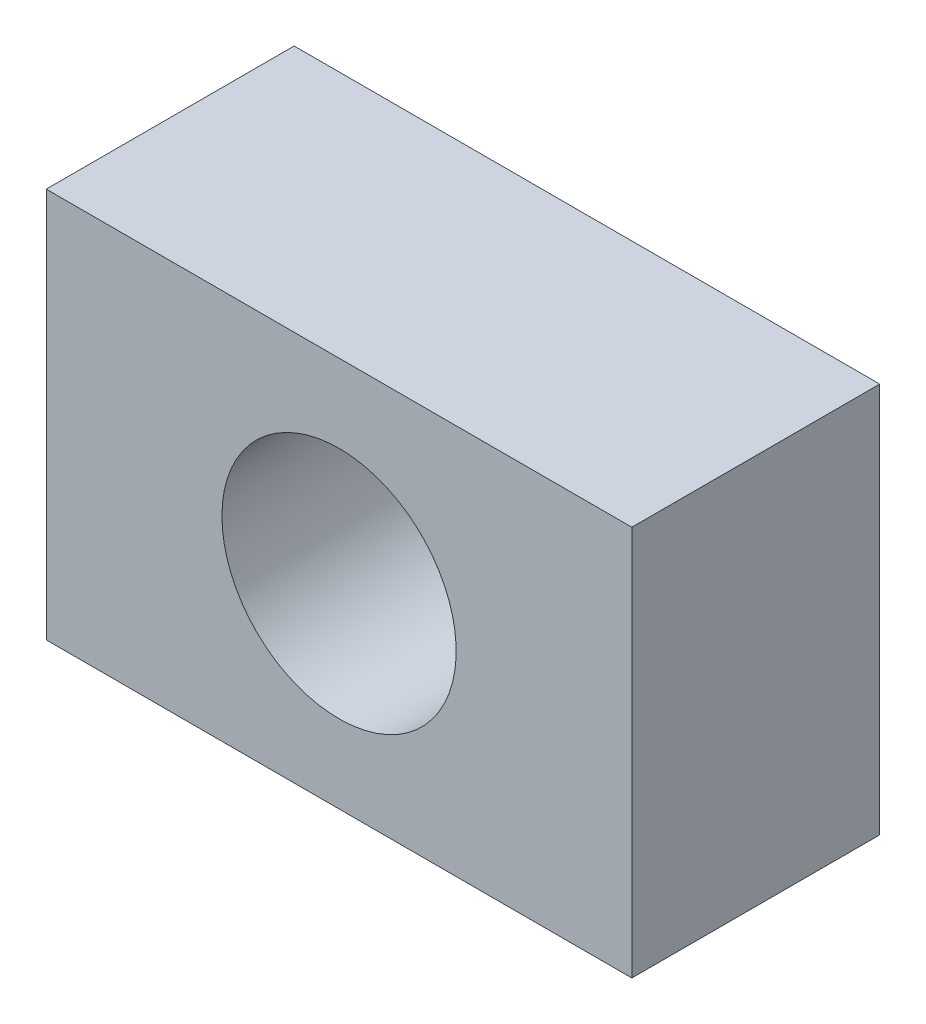
SolidWorks part; units mm, degrees
material "Alloy Steel"
ref_plane "Front Plane" through (0, 0, 0) normal (0, 0, 1) x (1, 0, 0)
ref_plane "Top Plane" through (0, 0, 0) normal (0, 1, 0) x (1, 0, 0)
ref_plane "Right Plane" through (0, 0, 0) normal (1, 0, 0) x (0, 0, -1)
sketch "Sketch1" plane through (0, 0, 0) normal (0, 0, 1) x (1, 0, 0)
  line L1 (-7.5, -5) -> (7.5, -5)
  line L2 (-7.5, -5) -> (-7.5, 5)
  line L3 (-7.5, 5) -> (7.5, 5)
  line L4 (7.5, -5) -> (7.5, 5)
  line L5 (-7.5, -5) -> (7.5, 5) construction
  line L6 (-7.5, 5) -> (7.5, -5) construction
  point P0 (0, 0)
  dimension "D1" = 10
  dimension "D2" = 15
extrude "Boss-Extrude1" add sketch "Sketch1" along normal blind 6.35
sketch "Sketch2" plane through (0, 0, 0) normal (0, 0, -1) x (-1, 0, 0)
  circle A0 centre (0, 0) radius 3
  dimension "D1" = 6
extrude "Cut-Extrude1" cut sketch "Sketch2" against normal through all
equation "\"Largeur\"= 10"
equation "\"Longueur\"= 15"
equation "\"Epaisseur\"= 6.35"
equation "\"D2@Sketch1\"=\"Longueur\""
equation "\"D1@Sketch1\"=\"Largeur\""
equation "\"D1@Boss-Extrude1\"= \"Epaisseur\""
equation "\"DiametreTrou\"= 6"
equation "\"D1@Sketch2\"=\"DiametreTrou\""
